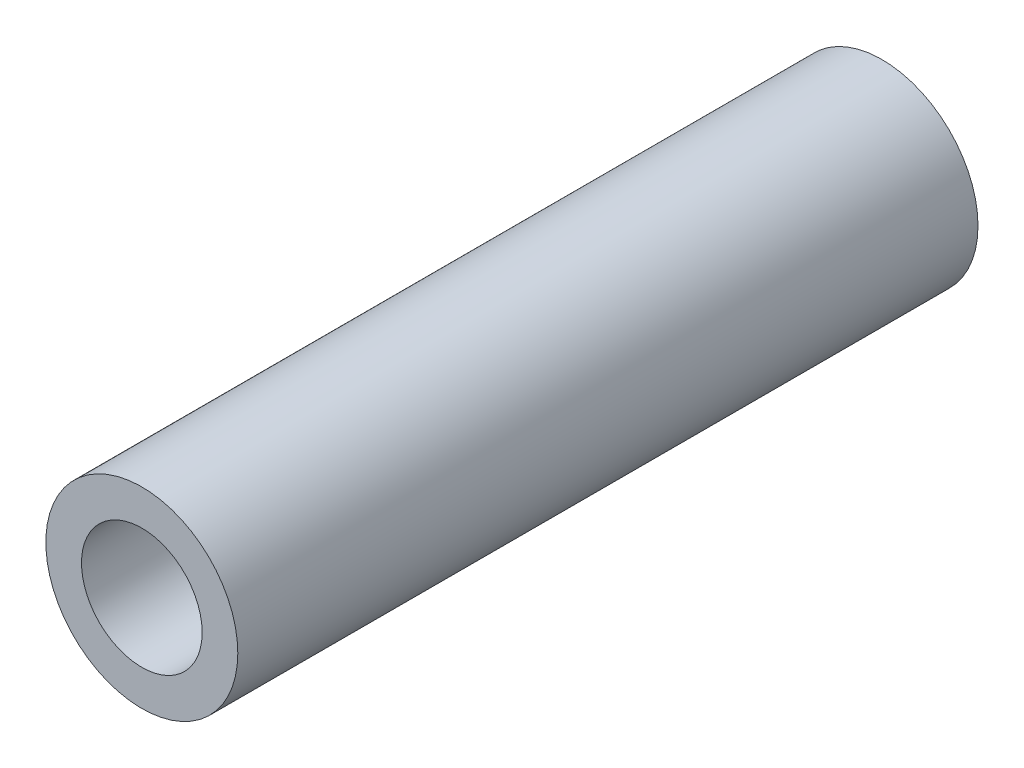
SolidWorks part; units mm, degrees
material "AISI 1020"
ref_plane "Спереди" through (0, 0, 0) normal (0, 0, 1) x (1, 0, 0)
ref_plane "Сверху" through (0, 0, 0) normal (0, 1, 0) x (1, 0, 0)
ref_plane "Справа" through (0, 0, 0) normal (1, 0, 0) x (0, 0, -1)
sketch "Эскиз1" plane through (0, 0, 0) normal (1, 0, 0) x (0, 0, -1)
  line L0 (-1000, 0) -> (49000, 0) construction
  line L1 (0, 0) -> (0, 7)
  line L2 (0, 7) -> (-26.99, 7)
  line L3 (-26.99, 13) -> (-26.99, -13) construction
  line L7 (-26.99, 7) -> (-26.99, 0)
  line L8 (-26.99, 0) -> (0, 0)
  line L10 (0, 7.5) -> (-24.99, 7.5) construction
  dimension "D1" = 0.5
revolve "Повернуть1" add sketch "Эскиз1" angle 360 about L0
hole_wizard "Отверстие обработанное метчиком M10x1.251" positions "Эскиз2" profile "Эскиз3" tap size "M10x1.25" standard "DIN"
sketch "Эскиз2" plane through (0, 0, 26.99) normal (0, 0, 1) x (1, 0, 0)
  point P0 (0, 0)
sketch "Эскиз3" plane through (0, 0, 26.99) normal (1, 0, 0) x (0, -1, 0)
  line L0 (0, 0) -> (0, 28.8938)
  line L1 (0, 28.8938) -> (4.4, 26.25)
  line L2 (4.4, 26.25) -> (4.4, 0)
  line L5 (4.4, 0) -> (0, 0)
  line L10 (0, 28.8938) -> (-4.4, 26.25) construction
  line L11 (0, -6.35) -> (0, 107.95) construction
  dimension "Диаметр сверла" = 8.8
  dimension "Глубина сверла" = 26.25
  dimension "Угол заточки сверла" = 118
cosmetic thread "Отверстие резьбы1" parameters "D1"=20, "D2"=10
mirror "Зеркальное отражение1" about plane through (0, 0, 0) normal (0, 0, 1) of bodies 104
